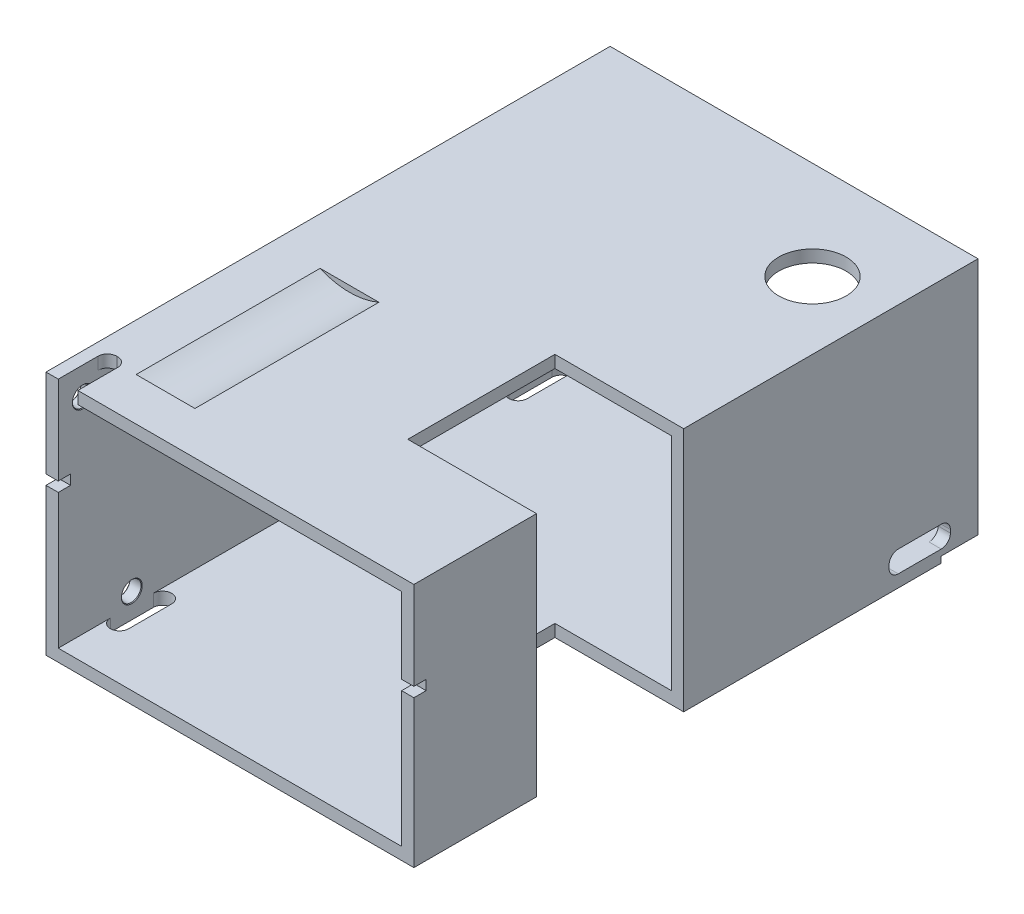
SolidWorks part; units mm, degrees
material "6063-T1"
ref_plane "Спереди" through (0, 0, 0) normal (0, 0, 1) x (1, 0, 0)
ref_plane "Сверху" through (0, 0, 0) normal (0, 1, 0) x (1, 0, 0)
ref_plane "Справа" through (0, 0, 0) normal (1, 0, 0) x (0, 0, -1)
sketch "Эскиз1" plane through (0, 0, 0) normal (0, 0, 1) x (1, 0, 0)
  line L0 (-28, -18) -> (-28, 18)
  line L1 (-30, -20) -> (30, -20)
  line L2 (-30, -20) -> (-30, 20)
  line L3 (-30, 20) -> (30, 20)
  line L4 (30, -20) -> (30, 20)
  line L5 (-30, -20) -> (30, 20) construction
  line L6 (-30, 20) -> (30, -20) construction
  line L7 (-28, 18) -> (28, 18)
  line L8 (28, -18) -> (28, 18)
  line L9 (-28, -18) -> (28, -18)
  point P0 (0, 0)
  dimension "D1" = 40
  dimension "D2" = 60
  dimension "D3" = 2
extrude "Бобышка-Вытянуть1" add sketch "Эскиз1" along normal blind 92
sketch "Эскиз2" plane through (0, 20, 0) normal (0, 1, 0) x (1, 0, 0)
  line L0 (28, 0) -> (28, -7)
  line L1 (30, 0) -> (-30, 0) construction
  line L2 (10, 0) -> (10, -7)
  line L4 (30, -92) -> (30, 0) construction
  arc A0 (28, -7) -> (10, -7) centre (19, -7) cw
  line M1 (30, 0) -> (-30, 0)
  dimension "D1" = 9
  dimension "D2" = 11
  dimension "D3" = 7
extrude "под_косой_ввод" [suppressed] cut sketch "Эскиз2" against normal up to next contours A0 L0 L2 M1
sketch "Эскиз3" plane through (0, 20, 0) normal (0, 1, 0) x (1, 0, 0)
  line L2 (30, -72) -> (9, -72)
  line L3 (9, -72) -> (9, -48)
  line L4 (9, -48) -> (30, -48)
  line L5 (30, -92) -> (30, 0) construction
  line L6 (30, 0) -> (-30, 0) construction
  line L7 (-30, -92) -> (-30, 0) construction
  dimension "D2" = 24
  dimension "D1" = 48
  dimension "D3" = 39
extrude "Вырез-Вытянуть2" cut sketch "Эскиз3" against normal through all
sketch "Эскиз9" plane through (0, -20, 0) normal (0, -1, 0) x (1, 0, 0)
  line L0 (30, 11) -> (28, 11) construction
  line L1 (30, 48) -> (30, 0) construction
  line L2 (30, 9.5) -> (28, 9.5)
  line L3 (30, 12.5) -> (28, 12.5)
  line L4 (-30, 0) -> (30, 0) construction
  line L5 (26.5, 11) -> (26.5, 0) construction
  arc A0 (30, 9.5) -> (30, 12.5) centre (30, 11) ccw
  arc A1 (28, 12.5) -> (28, 9.5) centre (28, 11) ccw
  circle A2 centre (21, 11) radius 3.25
  point P4 (29, 11)
  dimension "D1" = 1.5
  dimension "D4" = 6.5
  dimension "D5" = 9
  dimension "D2" = 11
  dimension "D3" = 3.5
extrude "Вырез-Вытянуть4" cut sketch "Эскиз9" against normal blind 4 contours A2
sketch "Эскиз10" plane through (30, 0, 0) normal (1, 0, 0) x (0, 0, -1)
  line L0 (-6, -14.5) -> (-13, -14.5)
  line L1 (-48, -18) -> (0, -18) construction
  line L2 (-14.5, -16) -> (-14.5, -16.5)
  line L3 (-13, -18) -> (-6, -18)
  line L6 (-4.5, -16) -> (-4.5, -16.5)
  line L8 (0, -20) -> (0, 20) construction
  arc A0 (-13, -18) -> (-14.5, -16.5) centre (-13, -16.5) cw
  arc A1 (-14.5, -16) -> (-13, -14.5) centre (-13, -16) cw
  arc A2 (-6, -18) -> (-4.5, -16.5) centre (-6, -16.5) ccw
  arc A3 (-6, -14.5) -> (-4.5, -16) centre (-6, -16) cw
  dimension "D1" = 1.5
  dimension "D2" = 10
  dimension "D3" = 3.5
  dimension "D4" = 4.5
extrude "Вырез-Вытянуть5" cut sketch "Эскиз10" against normal up to next
sketch "Эскиз11" plane through (0, 20, 0) normal (0, 1, 0) x (1, 0, 0)
  line L0 (-30, -92) -> (-30, 0) construction
  line L2 (30, 0) -> (-30, 0) construction
  line L8 (-10, -82) -> (-20, -82)
  line L9 (-7, -79) -> (-7, -66)
  line L10 (-10, -63) -> (-20, -63)
  line L11 (-23, -79) -> (-23, -66)
  arc A0 (-23, -66) -> (-20, -63) centre (-20, -66) cw
  arc A1 (-10, -63) -> (-7, -66) centre (-10, -66) cw
  arc A2 (-7, -79) -> (-10, -82) centre (-10, -79) cw
  arc A3 (-20, -82) -> (-23, -79) centre (-20, -79) cw
  dimension "D7" = 3
  dimension "D1" = 63
  dimension "D3" = 16
  dimension "D4" = 19
  dimension "D5" = 7
extrude "Вырез-Вытянуть6" [suppressed] cut sketch "Эскиз11" against normal up to next contours A3 L8 A2 L9 A1 L10 A0 L11
hole_wizard "Зенковка для винта с потайной головкой и внутренним шестигранником M31" [suppressed] positions "Эскиз14" profile "Эскиз13" countersink size "M3" standard "DIN"
sketch "Эскиз14" plane through (-30, 0, 0) normal (-1, 0, 0) x (0, 0, 1)
  line L0 (100, -20) -> (0, -20) construction
  line L1 (100, 3) -> (100, -20) construction
  point P1 (96, -1)
  point P4 (86, 3)
  point P7 (86, 13)
  dimension "D1" = 19
  dimension "D2" = 23
  dimension "D3" = 33
  dimension "D4" = 4
  dimension "D5" = 14
sketch "Эскиз13" plane through (-30, -1, 96) normal (0, 1, 0) x (0, 0, 1)
  line L0 (0, 0) -> (0, 2)
  line L1 (0, 2) -> (1.75, 2)
  line L2 (1.6, 1.85) -> (1.6, 1.15)
  line L3 (1.6, 1.15) -> (2.75, 0)
  line L5 (2.75, 0) -> (0, 0)
  line L6 (-1.6, 1.15) -> (-2.75, 0) construction
  line L7 (1.75, 2) -> (1.6, 1.85)
  line L8 (-1.75, 2) -> (-1.6, 1.85) construction
  line L11 (0, -6.35) -> (0, 107.95) construction
  dimension "Диаметр сквозного отверстия" = 3.2
  dimension "Глубина сквозного отверстия" = 2
  dimension "Диаметр передней зенковки" = 5.5
  dimension "Угол передней зенковки" = 90
  dimension "Диаметр задней зенковки" = 3.5
  dimension "Угол задней зенковки" = 90
sketch "Эскиз16" plane through (0, 0, 0) normal (0, 0, -1) x (-1, 0, 0)
  line L0 (-30, 20) -> (30, 20) construction
  line L1 (17.5, 19) -> (30, 19) construction
  line L2 (30, 20) -> (30, -20) construction
  line L3 (22.2958, 20) -> (12.7042, 20)
  arc A0 (22.2958, 20) -> (12.7042, 20) centre (17.5, 31) cw
  dimension "D2" = 12.5
  dimension "D3" = 12
  dimension "D1" = 1
extrude "Вырез-Вытянуть8" cut sketch "Эскиз16" against normal blind 30 from offset 55
sketch "Эскиз17" plane through (0, 20, 0) normal (0, 1, 0) x (1, 0, 0)
  line L0 (30, -48) -> (30, 0) construction
  line L1 (30, 0) -> (-30, 0) construction
  circle A0 centre (19, -16) radius 5.5
  dimension "D1" = 11
  dimension "D2" = 11
  dimension "D3" = 16
extrude "Вырез-Вытянуть9" cut sketch "Эскиз17" against normal up to next
sketch "Эскиз18" plane through (30, 0, 0) normal (1, 0, 0) x (0, 0, -1)
  line L0 (-6, -20) -> (-6, -19)
  line L1 (-48, -20) -> (0, -20) construction
  line L2 (-6, -19) -> (0, -19)
  line L3 (0, -20) -> (0, 20) construction
  line M12 (-48, -20) -> (0, -20)
  line M13 (0, -20) -> (0, 20)
  dimension "D1" = 1
  dimension "D2" = 6
extrude "Вырез-Вытянуть10" cut sketch "Эскиз18" against normal through all contours L2 L0 M12 M13
sketch "Эскиз19" plane through (0, 20, 0) normal (0, 1, 0) x (1, 0, 0)
  line L0 (-28, -92) -> (-28, -85.5)
  line L1 (30, -92) -> (-30, -92) construction
  line L2 (-26.5, -84) -> (-26.3, -84)
  line L3 (-24.8, -85.5) -> (-24.8, -92)
  line L4 (-28, -92) -> (-28, 0) construction
  arc A0 (-24.8, -85.5) -> (-26.3, -84) centre (-26.3, -85.5) ccw
  arc A1 (-26.5, -84) -> (-28, -85.5) centre (-26.5, -85.5) ccw
  line M10 (-30, -92) -> (30, -92)
  dimension "D3" = 1.5
  dimension "D1" = 3.2
  dimension "D2" = 8
extrude "Вырез-Вытянуть11" cut sketch "Эскиз19" against normal up to next contours L3 L2 L0 M10
hole_wizard "Отверстие с зазором M31" positions "Эскиз21" profile "Эскиз20" hole size "M3" standard "DIN" end condition up to next
sketch "Эскиз21" plane through (-30, 0, 0) normal (-1, 0, 0) x (0, 0, 1)
  line L0 (92, 20) -> (0, 20) construction
  line L1 (92, 20) -> (92, -20) construction
  line L2 (92, -20) -> (6, -20) construction
  line L3 (0, 20) -> (0, -19) construction
  point P0 (88, 15.5)
  point P6 (15, -16)
  point P8 (80, -16)
  dimension "D1" = 4.5
  dimension "D2" = 4
  dimension "D3" = 4
  dimension "D4" = 65
  dimension "D5" = 15
sketch "Эскиз20" plane through (-30, 15.5, 88) normal (0, 1, 0) x (0, 0, 1)
  line L0 (0, 0) -> (0, 2)
  line L1 (0, 2) -> (1.7, 2)
  line L2 (1.6, 1.9) -> (1.6, 0.1)
  line L3 (1.6, 0.1) -> (1.7, 0)
  line L5 (1.7, 0) -> (0, 0)
  line L6 (-1.6, 0.1) -> (-1.7, 0) construction
  line L7 (1.7, 2) -> (1.6, 1.9)
  line L8 (-1.7, 2) -> (-1.6, 1.9) construction
  line L11 (0, -6.35) -> (0, 107.95) construction
  dimension "Диаметр сквозного отверстия" = 3.2
  dimension "Глубина сквозного отверстия" = 2
  dimension "Диаметр передней зенковки" = 3.4
  dimension "Угол передней зенковки" = 90
  dimension "Диаметр задней зенковки" = 3.4
  dimension "Угол задней зенковки" = 90
sketch "Эскиз22" plane through (-30, 0, 0) normal (-1, 0, 0) x (0, 0, 1)
  line L0 (92, 5.6) -> (90, 5.6)
  line L1 (92, 20) -> (92, -20) construction
  line L2 (90, 5.6) -> (90, 4)
  line L3 (90, 4) -> (92, 4)
  line L4 (92, -20) -> (6, -20) construction
  dimension "D1" = 1.6
  dimension "D2" = 24
  dimension "D3" = 2
extrude "Вырез-Вытянуть12" cut sketch "Эскиз22" against normal through all
sketch "Эскиз23" plane through (0, -20, 0) normal (0, -1, 0) x (1, 0, 0)
  line L0 (-26.5, 83.5) -> (-26.5, 76.5) construction
  line L1 (-25, 83.5) -> (-25, 76.5)
  line L2 (-28, 83.5) -> (-28, 76.5)
  line L3 (-26.5, 11.5) -> (-26.5, 18.5) construction
  line L4 (-28, 11.5) -> (-28, 18.5)
  line L5 (-25, 11.5) -> (-25, 18.5)
  line L6 (-28, 92) -> (-28, 0) construction
  line L7 (-26.5, 85) -> (-30, 85) construction
  line L8 (-30, 92) -> (-30, 6) construction
  line L9 (-26.5, 75) -> (-30, 75) construction
  line L11 (-30, 0) -> (30, 0) construction
  arc A0 (-25, 83.5) -> (-28, 83.5) centre (-26.5, 83.5) ccw
  arc A1 (-28, 76.5) -> (-25, 76.5) centre (-26.5, 76.5) ccw
  arc A2 (-28, 11.5) -> (-25, 11.5) centre (-26.5, 11.5) ccw
  arc A3 (-25, 18.5) -> (-28, 18.5) centre (-26.5, 18.5) ccw
  point P2 (-26.5, 80)
  point P8 (-26.5, 15)
  dimension "D1" = 3
  dimension "D2" = 10
  dimension "D3" = 65
  dimension "D4" = 15
extrude "Вырез-Вытянуть13" cut sketch "Эскиз23" against normal up to next contours L5 A3 L4 A2 | L2 A1 L1 A0
